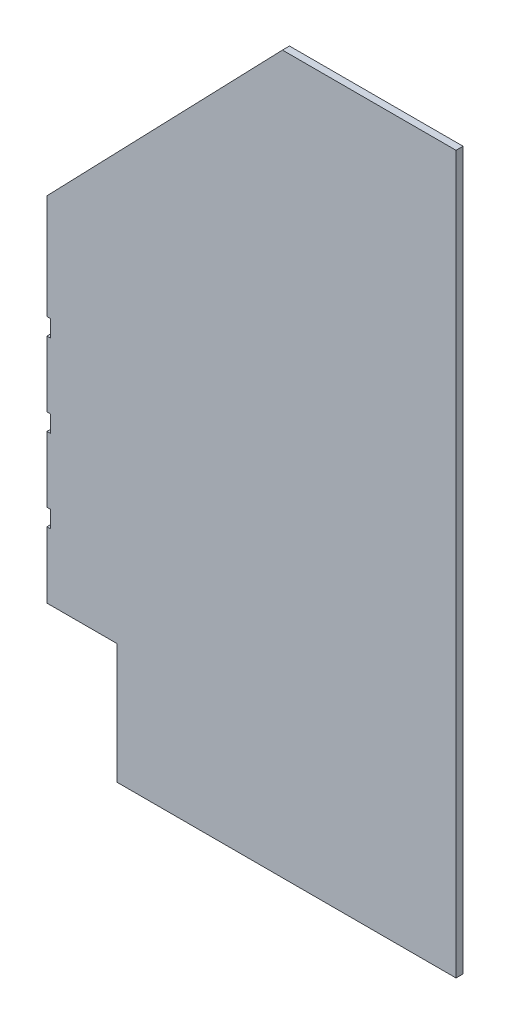
SolidWorks part; units mm, degrees
material "Pine"
ref_plane "Front Plane" through (0, 0, 0) normal (0, 0, 1) x (1, 0, 0)
ref_plane "Top Plane" through (0, 0, 0) normal (0, 1, 0) x (1, 0, 0)
ref_plane "Right Plane" through (0, 0, 0) normal (1, 0, 0) x (0, 0, -1)
sketch "Sketch1" plane through (0, 0, 0) normal (0, 0, 1) x (1, 0, 0)
  line L0 (-284.2347, -712.9318) -> (-284.2347, -116.0318) construction
  line L2 (-284.2347, -116.0318) -> (-284.2347, -712.9318)
  line L3 (-165.9659, -916.1318) -> (407.9153, -916.1318)
  line L4 (407.9153, 296.7182) -> (407.9153, -916.1318)
  line L7 (-284.2347, -712.9318) -> (-165.9659, -712.9318)
  line L8 (-165.9659, -916.1318) -> (-165.9659, -712.9318)
  line L10 (407.9153, 296.7182) -> (114.2278, 296.7182)
  line L11 (114.2278, 296.7182) -> (-284.2347, -116.0318)
  dimension "D1" = 118.2687
  dimension "D2" = 203.2
  dimension "D3" = 596.9
  dimension "D4" = 692.15
  dimension "D5" = 1212.85
  dimension "D6" = 293.6875
extrude "Boss-Extrude1" add sketch "Sketch1" along normal blind 11.9062
sketch "Sketch2" plane through (0, 0, 11.9062) normal (0, 0, 1) x (1, 0, 0)
  line L0 (-284.2347, -116.0318) -> (-284.2347, -712.9318) construction
  line L1 (-284.2347, -600.9813) -> (-277.8847, -600.9813)
  line L2 (-284.2347, -600.9813) -> (-284.2347, -572.4063)
  line L3 (-284.2347, -572.4063) -> (-277.8847, -572.4063)
  line L4 (-277.8847, -600.9813) -> (-277.8847, -572.4063)
  line L5 (-284.2347, -712.9318) -> (-165.9659, -712.9318) construction
  line L6 (-284.2347, -461.2813) -> (-277.8847, -461.2813)
  line L7 (-284.2347, -461.2813) -> (-284.2347, -432.7063)
  line L8 (-284.2347, -432.7063) -> (-277.8847, -432.7063)
  line L9 (-277.8847, -461.2813) -> (-277.8847, -432.7063)
  line L10 (-284.2347, -321.5813) -> (-277.8847, -321.5813)
  line L11 (-284.2347, -321.5813) -> (-284.2347, -293.0063)
  line L12 (-284.2347, -293.0063) -> (-277.8847, -293.0063)
  line L13 (-277.8847, -321.5813) -> (-277.8847, -293.0063)
  point P16 (-277.8847, -586.6938)
  point P17 (-277.8847, -446.9938)
  point P18 (-277.8847, -307.2938)
  dimension "D1" = 28.575
  dimension "D2" = 6.35
  dimension "D3" = 126.238
  dimension "D4" = 265.938
  dimension "D5" = 405.638
  dimension "D6" = 6.35
  dimension "D7" = 6.35
extrude "Cut-Extrude1" cut sketch "Sketch2" against normal through all
